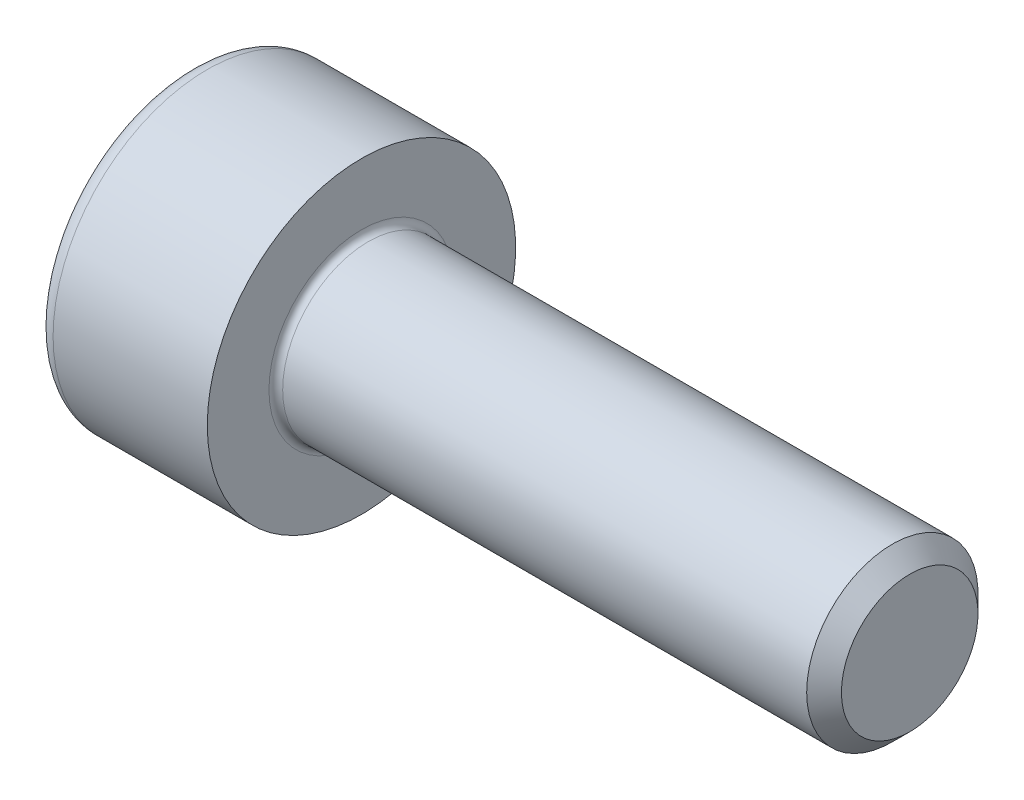
SolidWorks part; units mm, degrees
ref_plane "Plane1" through (0, 0, 0) normal (0, 0, 1) x (1, 0, 0)
ref_plane "Plane2" through (0, 0, 0) normal (0, 1, 0) x (1, 0, 0)
ref_plane "Plane3" through (0, 0, 0) normal (1, 0, 0) x (0, 0, -1)
sketch "BodySke" plane through (0, 0, 0) normal (0, 0, 1) x (1, 0, 0)
  line L0 (0, 0) -> (0, 2.25)
  line L1 (0, 2.25) -> (2.5, 2.25)
  line L2 (2.5, 2.25) -> (2.5, 1.25)
  line L3 (2.5, 1.25) -> (10.2465, 1.25)
  line L4 (10.5, 0.9965) -> (10.5, 0)
  line L5 (10.5, 0) -> (0, 0)
  line L6 (-31.75, 0) -> (127, 0) construction
  line L8 (10.5, 0.9965) -> (10.2465, 1.25)
  line L10 (10.5, -0.9965) -> (10.2465, -1.25) construction
  line L11 (2.95, 9.525) -> (2.95, 3.175) construction
  line L12 (2.5, 9.525) -> (2.5, 3.175) construction
  line L13 (-49.5, 9.525) -> (-49.5, 3.175) construction
  dimension "Diameter" = 2.5
  dimension "Head_ht" = 2.5
  dimension "Length" = 8
  dimension "Body_ch_ang" = 45
  dimension "Head_dia" = 4.5
  dimension "Minor_dia" = 1.993
  dimension "Advance" = 0.45
  dimension "Thread_nom" = 8
  dimension "Thread_length" = 60
revolve "Base-Revolve" add sketch "BodySke"
cosmetic thread "ThreadCosmetic"
fillet "Fillet1" radius 0.1 1 edges at (2.5, 0, 1.25)
fillet "Fillet2" radius 0.25 1 edges at (0, 0, 2.25)
sketch "Sketch2" plane through (0, 0, 0) normal (0, 0, 1) x (1, 0, 0)
  line L0 (0, 1.01) -> (1.1, 1.01)
  line L1 (1.1, 1.01) -> (1.6831, 0)
  line L2 (-31.75, 0) -> (127, 0) construction
  line L3 (1.6831, 0) -> (0, 0)
  line L4 (0, 0) -> (0, 1.01)
  line L6 (0, 0) -> (47.625, 0) construction
  dimension "D1" = 1.01
  dimension "D2" = 60
  dimension "Depth" = 1.1
revolve "Hex-PreBroach" cut sketch "Sketch2" angle 360 about L6
sketch "Sketch3" plane through (0, 0, 0) normal (-1, 0, 0) x (0, 0.5, 0.866)
  line L0 (0.5831, 1.01) -> (-0.5831, 1.01)
  line L1 (-0.5831, 1.01) -> (-1.1662, 0)
  line L2 (0.5831, 1.01) -> (1.1662, 0)
  line L3 (0.5831, -1.01) -> (1.1662, 0)
  line L4 (0.5831, -1.01) -> (-0.5831, -1.01)
  line L5 (-0.5831, -1.01) -> (-1.1662, 0)
  dimension "D1" = 1.01
  dimension "D2" = 1.01
  dimension "Hex_size" = 2.02
extrude "Hex" cut sketch "Sketch3" against normal blind 1.1
sketch "ThdSchSke" plane through (0, 0, 0) normal (0, 0, 1) x (1, 0, 0)
  line L0 (3.85, -0.9965) -> (3.6725, -1.25)
  line L1 (3.85, -0.9965) -> (4.0275, -1.25)
  line L2 (4.0275, -1.25) -> (4.0275, -1.5625)
  line L3 (-3.175, 0) -> (5.1513, 0) construction
  line L4 (0, 2) -> (0, -2) construction
  line L5 (4.0275, -1.5625) -> (3.6725, -1.5625)
  line L6 (3.6725, -1.5625) -> (3.6725, -1.25)
  dimension "Thread_minor" = 1.993
  dimension "Diameter" = 2.5
  dimension "Start" = 3.85
  dimension "SideAngle" = 55
  dimension "VeeAngle" = 70
  dimension "Overcut" = 3.125
revolve "ThreadSchematic" [suppressed] cut sketch "ThdSchSke" angle 360 about L3
pattern_linear "ThdSchPat" [suppressed]
equation "\"D2@Sketch3\" = \"Hex_size@Sketch3\" / 2"
equation "\"D1@Sketch3\" = \"Hex_size@Sketch3\" / 2"
equation "\"D1@Sketch2\" = \"Hex_size@Sketch3\" / 2"
equation "\"Thread_minor@ThreadCosmetic\"  =  \"Minor_dia@BodySke\""
equation "\"Depth@Sketch2\" =  \"Key_eng@Hex\""
equation "\"Thread_length@ThreadCosmetic\" = ((sgn( (\"Length@BodySke\" - \"Advance@BodySke\" * 3.0) - \"Thread_nom@BodySke\" )-1)*( (\"Length@BodySke\" - \"Advance@BodySke\" * 3.0) - \"Thread_nom@BodySke\" ))/-2+ \"Thread_nom@BodySke\""
equation "\"Thread_minor@ThdSchSke\" = \"Minor_dia@BodySke\""
equation "\"Diameter@ThdSchSke\" = \"Diameter@BodySke\""
equation "\"Overcut@ThdSchSke\" = \"Diameter@BodySke\" * 1.25"
equation "\"Start@ThdSchSke\" = \"Head_ht@BodySke\" + \"Length@BodySke\" - \"Thread_length@ThreadCosmetic\"  '---Non-countersunk---"
equation "\"Num_threads@ThdSchPat\" = int( \"Thread_length@ThreadCosmetic\" / \"Advance@BodySke\" + 0.999 )  + 1"
equation "\"Advance@ThdSchPat\" = \"Thread_length@ThreadCosmetic\" /  (\"Num_threads@ThdSchPat\" - 1) 'relax it"
equation "\"Num_threads@ThdSchPat\" = \"Num_threads@ThdSchPat\" - sgn( \"Num_threads@ThdSchPat\" - 1) '---chamfered tips only---"
